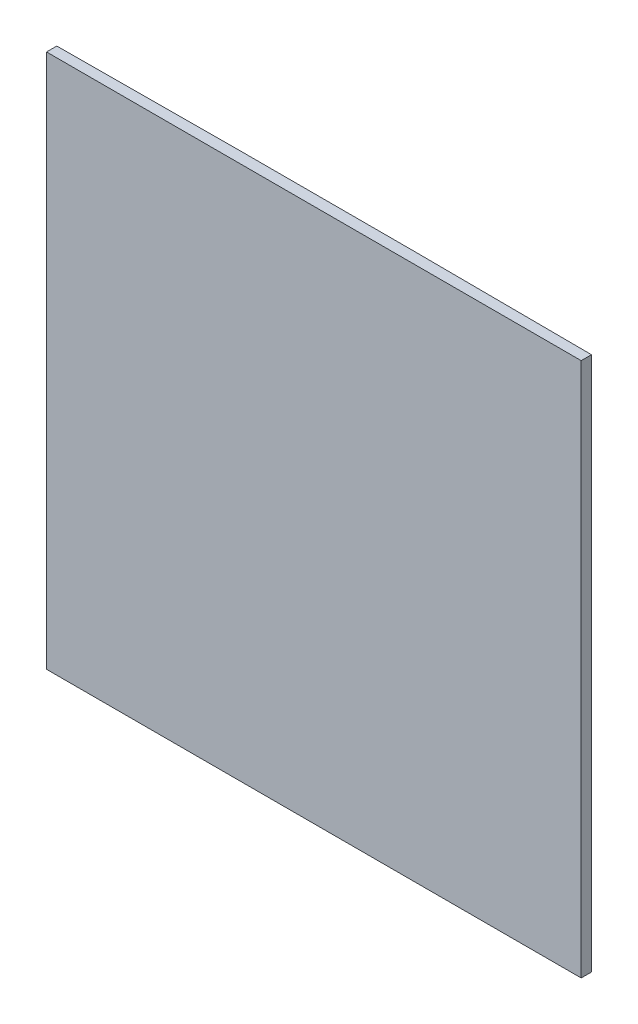
SolidWorks part; units mm, degrees
ref_plane "Front" through (0, 0, 0) normal (0, 0, 1) x (1, 0, 0)
ref_plane "Top" through (0, 0, 0) normal (0, 1, 0) x (1, 0, 0)
ref_plane "Right" through (0, 0, 0) normal (1, 0, 0) x (0, 0, -1)
sketch "Sketch1" plane through (0, 0, 0) normal (0, 1, 0) x (1, 0, 0)
  line L0 (0, 0) -> (52, 0)
  line L1 (52, 0) -> (52, 1)
  line L2 (0, 1) -> (0, 0)
  arc A0 (52, 1) -> (0, 1) centre (26, -3378.95) ccw
  dimension "D3" = 1.1
  dimension "D1" = 1
  dimension "D2" = 52
extrude "Boss-Extrude1" add sketch "Sketch1" along normal blind 52
